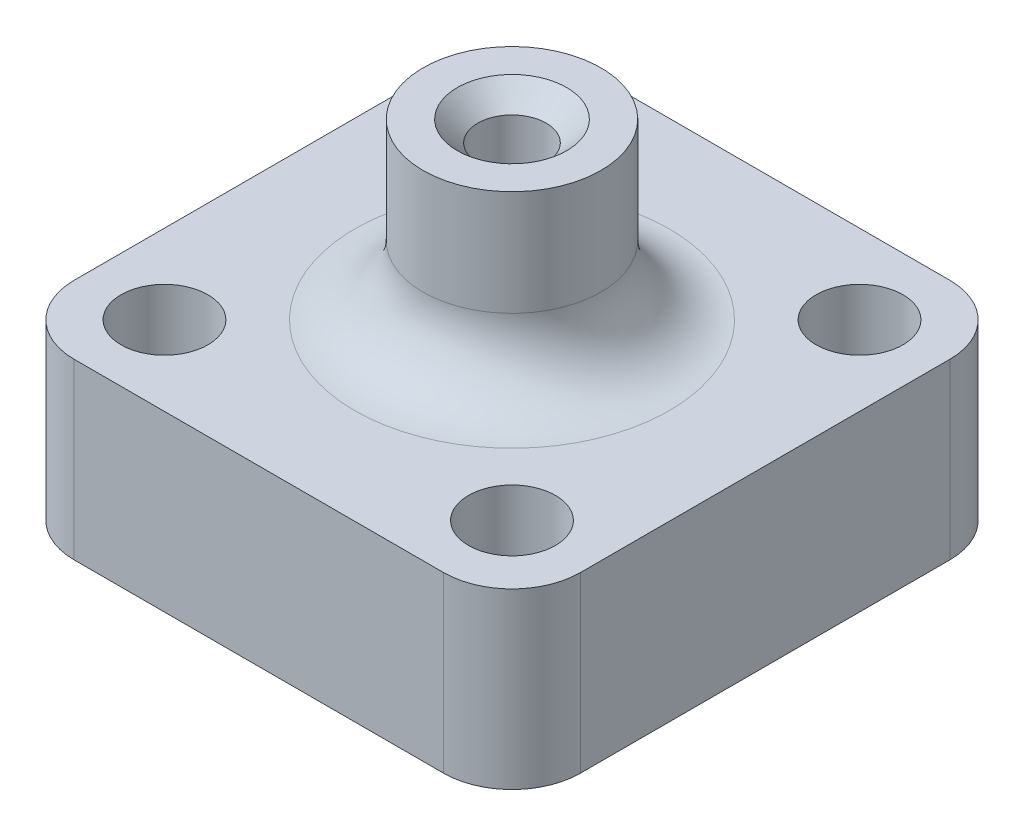
SolidWorks part; units mm, degrees
ref_plane "Front" through (0, 0, 0) normal (0, 0, 1) x (1, 0, 0)
ref_plane "Top" through (0, 0, 0) normal (0, 1, 0) x (1, 0, 0)
ref_plane "Right" through (0, 0, 0) normal (1, 0, 0) x (0, 0, -1)
sketch "Sketch1" plane through (0, 0, 0) normal (0, 1, 0) x (1, 0, 0)
  line L1 (-18.5, 18.5) -> (18.5, 18.5)
  line L2 (-18.5, 18.5) -> (-18.5, -18.5)
  line L3 (-18.5, -18.5) -> (18.5, -18.5)
  line L4 (18.5, 18.5) -> (18.5, -18.5)
  line L5 (-18.5, 18.5) -> (18.5, -18.5) construction
  line L6 (-18.5, -18.5) -> (18.5, 18.5) construction
  circle A0 centre (0, 0) radius 2.5
  circle A1 centre (-12.7, -12.7) radius 3.175
  circle A2 centre (12.7, -12.7) radius 3.175
  circle A3 centre (12.7, 12.7) radius 3.175
  circle A4 centre (-12.7, 12.7) radius 3.175
  point P0 (0, 0)
  point P16 (0, 0)
  point P17 (0, 0)
  point P18 (0, 0)
  dimension "D2" = 6.35
  dimension "D5" = 5
  dimension "D1" = 37
  dimension "D3" = 25.4
  dimension "D4" = 25.4
extrude "Boss-Extrude1" add sketch "Sketch1" along normal blind 12.7
sketch "Sketch2" plane through (0, 12.7, 0) normal (0, 1, 0) x (1, 0, 0)
  circle A0 centre (0, 0) radius 6.5
  circle A1 centre (0, 0) radius 2.5
  dimension "D1" = 5
  dimension "D2" = 13
extrude "Boss-Extrude2" add sketch "Sketch2" along normal blind 12.7
fillet "Fillet1" radius 5 5 edges at (0, 12.7, 6.5) (-18.5, 6.35, -18.5) (18.5, 6.35, -18.5) (18.5, 6.35, 18.5) (-18.5, 6.35, 18.5)
chamfer "Chamfer1" distance 1.5 angle 45 1 edges at (0, 25.4, 2.5)
